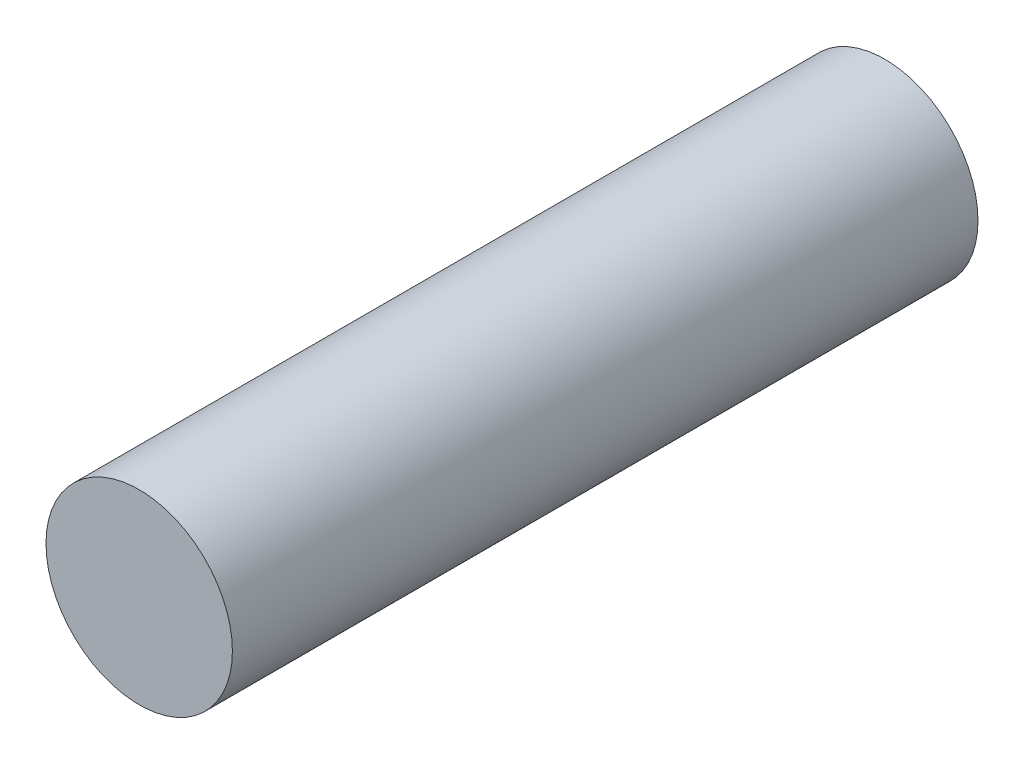
SolidWorks part; units mm, degrees
ref_plane "前基準面" through (0, 0, 0) normal (0, 0, 1) x (1, 0, 0)
ref_plane "上基準面" through (0, 0, 0) normal (0, 1, 0) x (1, 0, 0)
ref_plane "右基準面" through (0, 0, 0) normal (1, 0, 0) x (0, 0, -1)
sketch "草圖1" plane through (0, 0, 0) normal (0, 0, 1) x (1, 0, 0)
  circle A0 centre (0, 0) radius 0.75
  dimension "D1" = 1.5
extrude "填料-伸長1" add sketch "草圖1" along normal mid plane 6
